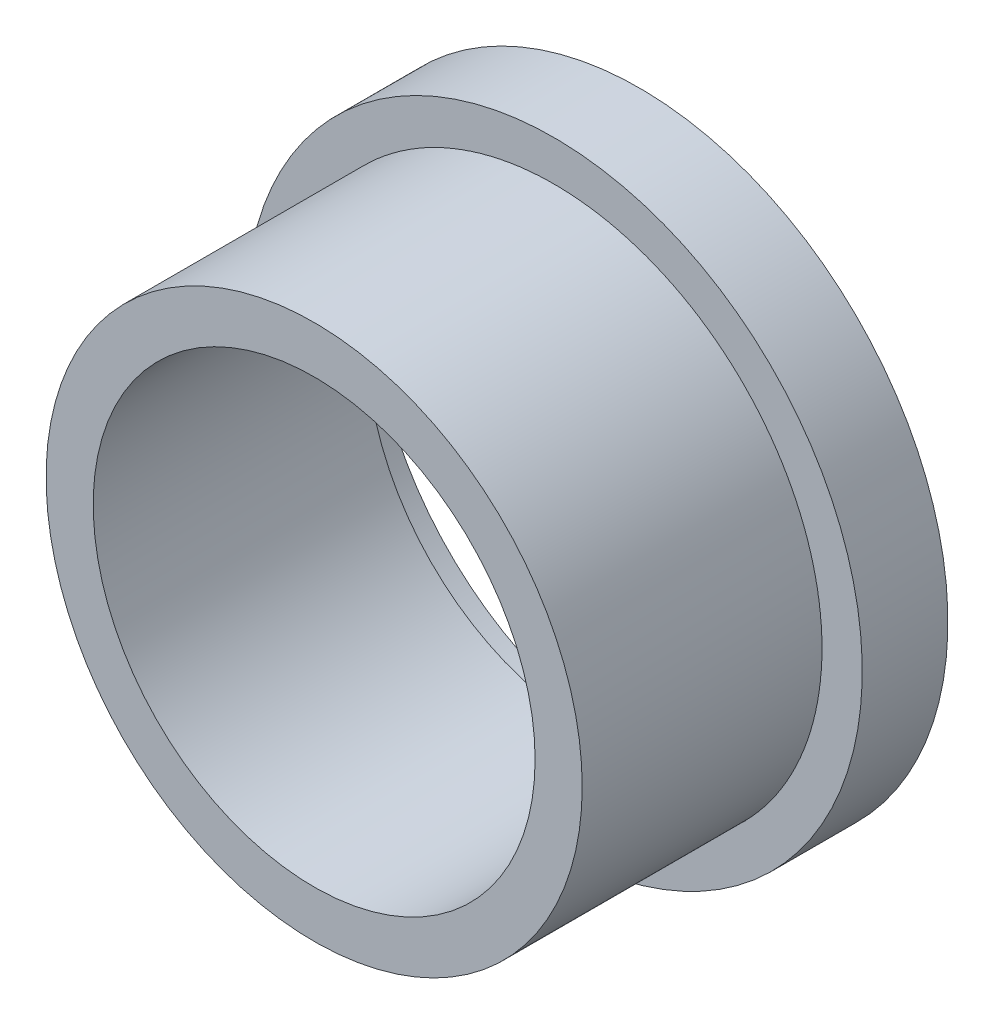
SolidWorks part; units mm, degrees
ref_plane "Front Plane" through (0, 0, 0) normal (0, 0, 1) x (1, 0, 0)
ref_plane "Top Plane" through (0, 0, 0) normal (0, 1, 0) x (1, 0, 0)
ref_plane "Right Plane" through (0, 0, 0) normal (1, 0, 0) x (0, 0, -1)
sketch "Sketch1" plane through (0, 0, 0) normal (0, 0, 1) x (1, 0, 0)
  circle A0 centre (0, 0) radius 6.45
  circle A1 centre (0, 0) radius 7.825
  dimension "D1" = 12.9
  dimension "D2" = 15.65
extrude "Boss-Extrude1" add sketch "Sketch1" along normal blind 8
sketch "Sketch2" plane through (0, 0, 0) normal (0, 0, -1) x (-1, 0, 0)
  circle A0 centre (0, 0) radius 7.825
  circle A1 centre (0, 0) radius 9
  circle A2 centre (0, 0) radius 7.825 construction
  dimension "D2" = 18
extrude "Boss-Extrude2" add sketch "Sketch2" along normal blind 1.5 and the other way blind 1 separate body
